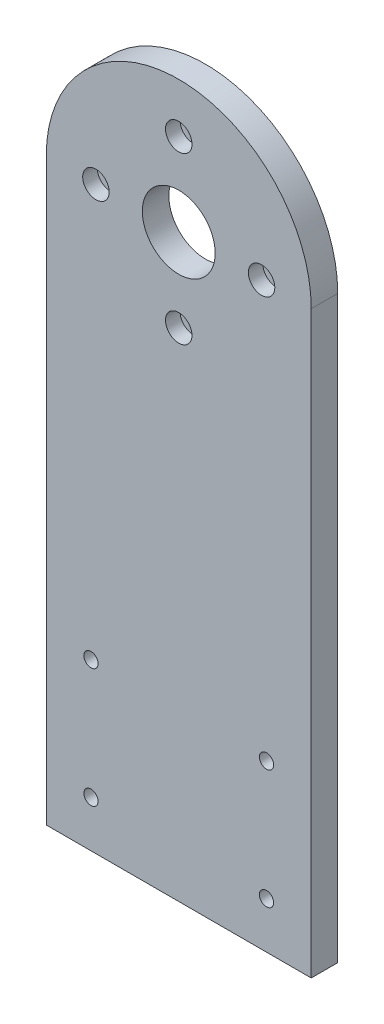
SolidWorks part; units mm, degrees
material "1060 Alloy"
ref_plane "Front" through (0, 0, 0) normal (0, 0, 1) x (1, 0, 0)
ref_plane "Top" through (0, 0, 0) normal (0, 1, 0) x (1, 0, 0)
ref_plane "Right" through (0, 0, 0) normal (1, 0, 0) x (0, 0, -1)
sketch "Sketch1" plane through (0, 0, 0) normal (0, 0, 1) x (1, 0, 0)
  line L1 (0, 0) -> (-80, 0)
  line L2 (0, 0) -> (0, 175)
  line L4 (-80, 0) -> (-80, 175)
  arc A0 (0, 175) -> (-80, 175) centre (-40, 175) ccw
  circle A1 centre (-40, 175) radius 8
  dimension "D1" = 16
  dimension "D2" = 175
extrude "Boss-Extrude1" add sketch "Sketch1" along normal blind 8
sketch "Sketch8" plane through (0, 0, 8) normal (0, 0, 1) x (1, 0, 0)
  circle A0 centre (-40, 175) radius 14.6853
hole_wizard "CBORE for M4 Hex Socket Head Cap Screw2" positions "Sketch3" profile "Sketch2" counterbore size "M4" standard "ISO" end condition through all
sketch "Sketch3" plane through (0, 0, 8) normal (0, 0, 1) x (1, 0, 0)
  line L0 (-40, 200) -> (-40, 150)
  circle A1 centre (-40, 175) radius 14.6853 construction
  point P18 (-40, 200)
  point P28 (-15, 175)
  point P29 (-40, 150)
  point P30 (-65, 175)
  dimension "D1" = 4
  dimension "D2" = 25
  dimension "D3" = 25
sketch "Sketch2" plane through (-40, 200, 8) normal (1, 0, 0) x (0, -1, 0)
  line L0 (0, 0) -> (0, 8)
  line L1 (0, 8) -> (2.15, 8)
  line L3 (2.15, 8) -> (2.15, 4.4)
  line L4 (2.15, 4.4) -> (4, 4.4)
  line L5 (4, 4.4) -> (4, 0)
  line L7 (4, 0) -> (0, 0)
  line L11 (0, -6.35) -> (0, 107.95) construction
  dimension "Thru Hole Dia." = 4.3
  dimension "Thru Hole Depth" = 8
  dimension "C'Bore Dia." = 8
  dimension "C'Bore Depth" = 4.4
hole_wizard "Ø20.0mm Transitional Dowel Hole1" positions "Sketch5" profile "Sketch4" hole size "Ø20.0" standard "ISO" end condition through all
sketch "Sketch5" plane through (0, 0, 8) normal (0, 0, 1) x (1, 0, 0)
  point P0 (-40, 175)
sketch "Sketch4" plane through (-40, 175, 8) normal (1, 0, 0) x (0, -1, 0)
  line L0 (0, 0) -> (0, 8)
  line L1 (0, 8) -> (11, 8)
  line L2 (11, 8) -> (11, 0)
  line L5 (11, 0) -> (0, 0)
  line L11 (0, -6.35) -> (0, 107.95) construction
  dimension "Thru Hole Dia." = 22
  dimension "Thru Hole Depth" = 8
hole_wizard "M4 Clearance Hole2" positions "Sketch7" profile "Sketch6" hole size "M4" standard "ISO" end condition through all
sketch "Sketch7" plane through (0, 0, 8) normal (0, 0, 1) x (1, 0, 0)
  line L3 (0, 0) -> (0, 175) construction
  line L4 (-80, 0) -> (0, 0) construction
  line L5 (-80, 175) -> (-80, 0) construction
  point P0 (-66.5, 50)
  point P3 (-13.5, 14)
  point P6 (-66.5, 14)
  point P19 (-13.5, 50)
  dimension "D1" = 13.5
  dimension "D3" = 0
  dimension "D4" = 36
  dimension "D5" = 36
  dimension "D6" = 0
  dimension "D7" = 13.5
  dimension "D8" = 14
sketch "Sketch6" plane through (-66.5, 50, 8) normal (1, 0, 0) x (0, -1, 0)
  line L0 (0, 0) -> (0, 8)
  line L1 (0, 8) -> (2.15, 8)
  line L2 (2.15, 8) -> (2.15, 0)
  line L5 (2.15, 0) -> (0, 0)
  line L11 (0, -6.35) -> (0, 107.95) construction
  dimension "Thru Hole Dia." = 4.3
  dimension "Thru Hole Depth" = 8
